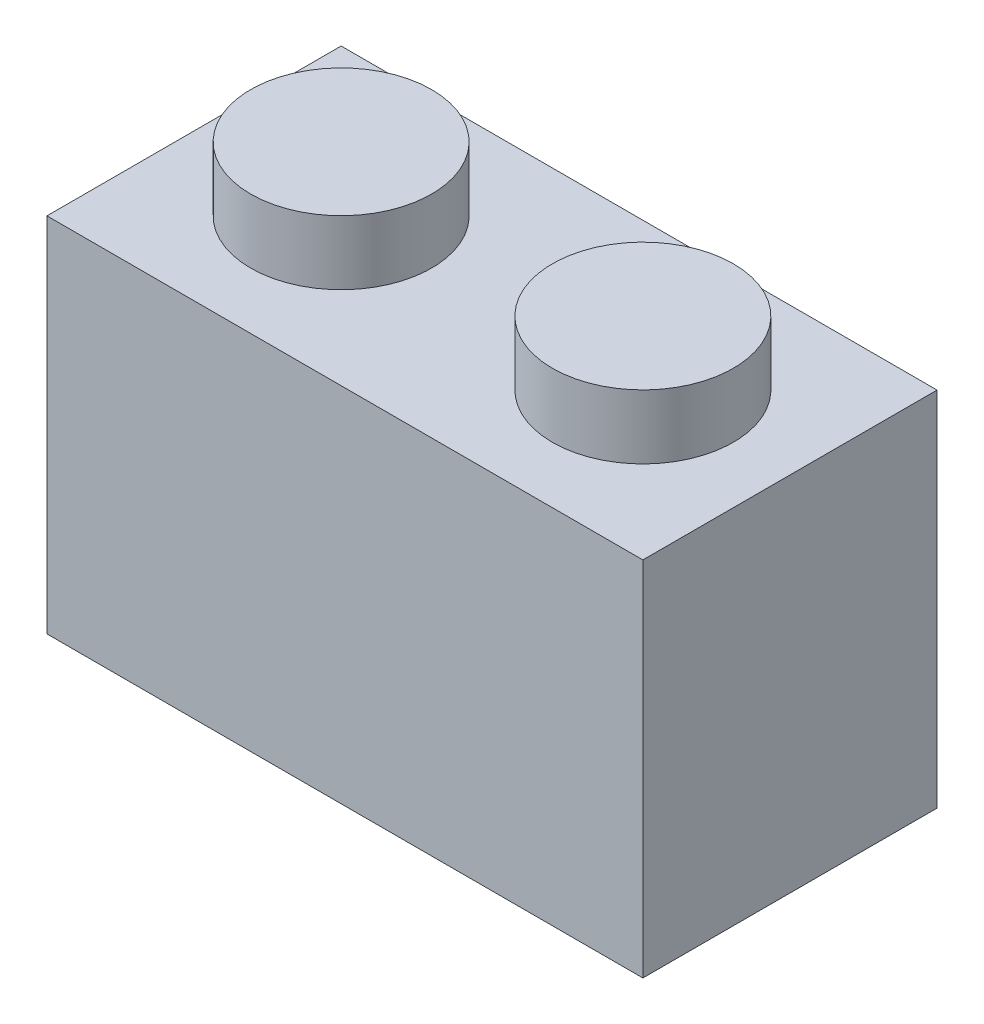
SolidWorks part; units mm, degrees
ref_plane "Спереди" through (0, 0, 0) normal (0, 0, 1) x (1, 0, 0)
ref_plane "Сверху" through (0, 0, 0) normal (0, 1, 0) x (1, 0, 0)
ref_plane "Справа" through (0, 0, 0) normal (1, 0, 0) x (0, 0, -1)
sketch "Эскиз1" plane through (0, 0, 0) normal (0, 1, 0) x (1, 0, 0)
  line L1 (0, 0) -> (15.8, 0)
  line L2 (0, 0) -> (0, 7.8)
  line L3 (0, 7.8) -> (15.8, 7.8)
  line L4 (15.8, 0) -> (15.8, 7.8)
  dimension "D1" = 15.8
  dimension "D2" = 7.8
extrude "Бобышка-Вытянуть1" add sketch "Эскиз1" along normal blind 9.6 contours L2 L1 L4 L3
sketch "Эскиз2" plane through (0, 9.6, 0) normal (0, 1, 0) x (1, 0, 0)
  line L0 (0, 7.8) -> (15.8, 7.8) construction
  line L1 (0, 0) -> (0, 7.8) construction
  circle A0 centre (3.9, 3.9) radius 2.4
  circle A1 centre (11.9, 3.9) radius 2.4
  dimension "D1" = 4.8
  dimension "D2" = 3.9
  dimension "D3" = 3.9
  dimension "D4" = 2
extrude "Бобышка-Вытянуть2" add sketch "Эскиз2" along normal blind 1.7
sketch "Эскиз3" plane through (0, 0, 0) normal (0, -1, 0) x (1, 0, 0)
  line L0 (15.8, 0) -> (15.8, -7.8) construction
  line L1 (0, 0) -> (15.8, 0) construction
  circle A0 centre (11.9, -3.9) radius 2.5
  circle A1 centre (3.9, -3.9) radius 2.5
  dimension "D1" = 5
  dimension "D2" = 3.9
  dimension "D3" = 3.9
  dimension "D4" = 2
extrude "Вырез-Вытянуть1" cut sketch "Эскиз3" against normal blind 1.8
